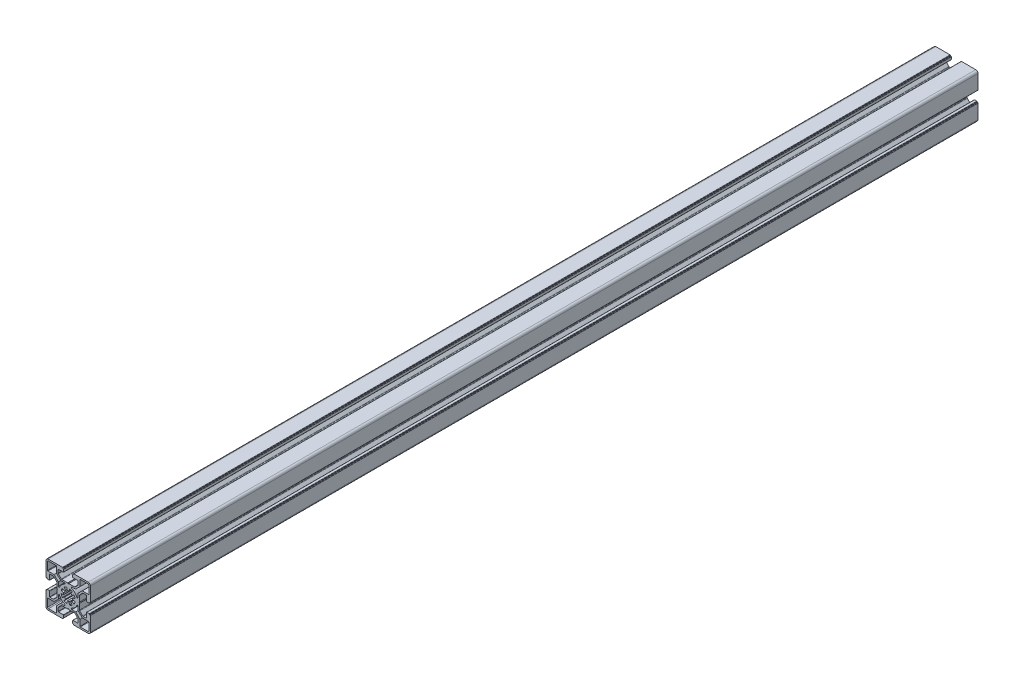
SolidWorks part; units mm, degrees
material "6063 T5"
ref_plane "Спереди" through (0, 0, 0) normal (0, 0, 1) x (1, 0, 0)
ref_plane "Сверху" through (0, 0, 0) normal (0, 1, 0) x (1, 0, 0)
ref_plane "Справа" through (0, 0, 0) normal (1, 0, 0) x (0, 0, -1)
sketch "Эскиз2" plane through (0, 0, 0) normal (0, 0, 1) x (1, 0, 0)
  line L0 (0, 0) -> (-23.2, 23.2) construction
  line L1 (-11.1, 8.413) -> (-11.1, 4.1569)
  line L2 (-11.1, 8.413) -> (-15.887, 13.2)
  line L3 (-8.413, 11.1) -> (-13.2, 15.887)
  line L4 (-8.413, 11.1) -> (-4.1569, 11.1)
  line L17 (-25, 11.3) -> (-25, 22.5)
  line L18 (-22.5, 25) -> (-11.3, 25)
  line L19 (11.3, 25) -> (22.5, 25)
  line L20 (25, 22.5) -> (25, 11.3)
  line L21 (25, -11.3) -> (25, -22.5)
  line L22 (22.5, -25) -> (11.3, -25)
  line L23 (-11.3, -25) -> (-22.5, -25)
  line L24 (-25, -22.5) -> (-25, -11.3)
  line L25 (-25.0176, 33.1253) -> (24.9824, 33.1253) construction
  line L26 (-15.887, 13.2) -> (-22.7, 13.2)
  line L27 (-23.2, 13.7) -> (-23.2, 22.2)
  line L28 (-22.2, 23.2) -> (-13.7, 23.2)
  line L29 (-13.2, 22.7) -> (-13.2, 15.887)
  line L30 (22.7, 13.2) -> (15.887, 13.2)
  line L31 (11.1, 8.413) -> (15.887, 13.2) [skipped]
  line L32 (11.1, 8.413) -> (11.1, 4.1569) [skipped]
  line L33 (8.413, 11.1) -> (4.1569, 11.1) [skipped]
  line L34 (8.413, 11.1) -> (13.2, 15.887) [skipped]
  line L35 (8.413, -11.1) -> (13.2, -15.887) [skipped]
  line L36 (8.413, -11.1) -> (4.1569, -11.1) [skipped]
  line L37 (11.1, -8.413) -> (11.1, -4.1569) [skipped]
  line L38 (11.1, -8.413) -> (15.887, -13.2) [skipped]
  line L39 (-11.1, -8.413) -> (-15.887, -13.2) [skipped]
  line L40 (-11.1, -8.413) -> (-11.1, -4.1569) [skipped]
  line L41 (-8.413, -11.1) -> (-4.1569, -11.1) [skipped]
  line L42 (-8.413, -11.1) -> (-13.2, -15.887) [skipped]
  line L43 (11.1, 8.413) -> (15.887, 13.2)
  line L44 (11.1, 8.413) -> (11.1, 4.1569)
  line L45 (8.413, 11.1) -> (4.1569, 11.1)
  line L46 (8.413, 11.1) -> (13.2, 15.887)
  line L47 (13.2, 15.887) -> (13.2, 22.7)
  line L48 (13.7, 23.2) -> (22.2, 23.2)
  line L49 (23.2, 22.2) -> (23.2, 13.7)
  line L50 (13.2, -22.7) -> (13.2, -15.887)
  line L51 (8.413, -11.1) -> (13.2, -15.887)
  line L52 (8.413, -11.1) -> (4.1569, -11.1)
  line L53 (11.1, -8.413) -> (11.1, -4.1569)
  line L54 (11.1, -8.413) -> (15.887, -13.2)
  line L55 (15.887, -13.2) -> (22.7, -13.2)
  line L56 (23.2, -13.7) -> (23.2, -22.2)
  line L57 (22.2, -23.2) -> (13.7, -23.2)
  line L58 (-22.7, -13.2) -> (-15.887, -13.2)
  line L59 (-11.1, -8.413) -> (-15.887, -13.2)
  line L60 (-11.1, -8.413) -> (-11.1, -4.1569)
  line L61 (-8.413, -11.1) -> (-4.1569, -11.1)
  line L62 (-8.413, -11.1) -> (-13.2, -15.887)
  line L63 (-13.2, -15.887) -> (-13.2, -22.7)
  line L64 (-13.7, -23.2) -> (-22.2, -23.2)
  line L65 (-23.2, -22.2) -> (-23.2, -13.7)
  arc A2 (-3.8971, 9.75) -> (-9.75, 3.8971) centre (0, 0) ccw
  arc A3 (-9.75, 3.8971) -> (-11.1, 4.1569) centre (-10.4, 4.1569) cw
  arc A5 (-3.8971, 9.75) -> (-4.1569, 11.1) centre (-4.1569, 10.4) ccw
  arc A18 (-25, 22.5) -> (-22.5, 25) centre (-22.5, 22.5) cw
  arc A19 (22.5, 25) -> (25, 22.5) centre (22.5, 22.5) cw
  arc A20 (25, -22.5) -> (22.5, -25) centre (22.5, -22.5) cw
  arc A21 (-22.5, -25) -> (-25, -22.5) centre (-22.5, -22.5) cw
  arc A22 (-23.2, 22.2) -> (-22.2, 23.2) centre (-22.2, 22.2) cw
  arc A23 (-13.7, 23.2) -> (-13.2, 22.7) centre (-13.7, 22.7) cw
  arc A24 (-22.7, 13.2) -> (-23.2, 13.7) centre (-22.7, 13.7) cw
  arc A25 (9.75, 3.8971) -> (11.1, 4.1569) centre (10.4, 4.1569) ccw [skipped]
  arc A26 (9.75, 3.8971) -> (3.8971, 9.75) centre (0, 0) ccw [skipped]
  arc A27 (3.8971, 9.75) -> (4.1569, 11.1) centre (4.1569, 10.4) cw [skipped]
  arc A28 (3.8971, -9.75) -> (4.1569, -11.1) centre (4.1569, -10.4) ccw [skipped]
  arc A29 (3.8971, -9.75) -> (9.75, -3.8971) centre (0, 0) ccw [skipped]
  arc A30 (9.75, -3.8971) -> (11.1, -4.1569) centre (10.4, -4.1569) cw [skipped]
  arc A31 (-9.75, -3.8971) -> (-11.1, -4.1569) centre (-10.4, -4.1569) ccw [skipped]
  arc A32 (-9.75, -3.8971) -> (-3.8971, -9.75) centre (0, 0) ccw [skipped]
  arc A33 (-3.8971, -9.75) -> (-4.1569, -11.1) centre (-4.1569, -10.4) cw [skipped]
  arc A34 (9.75, 3.8971) -> (11.1, 4.1569) centre (10.4, 4.1569) ccw
  arc A35 (9.75, 3.8971) -> (3.8971, 9.75) centre (0, 0) ccw
  arc A36 (3.8971, 9.75) -> (4.1569, 11.1) centre (4.1569, 10.4) cw
  arc A37 (13.2, 22.7) -> (13.7, 23.2) centre (13.7, 22.7) cw
  arc A38 (22.2, 23.2) -> (23.2, 22.2) centre (22.2, 22.2) cw
  arc A39 (23.2, 13.7) -> (22.7, 13.2) centre (22.7, 13.7) cw
  arc A40 (3.8971, -9.75) -> (4.1569, -11.1) centre (4.1569, -10.4) ccw
  arc A41 (3.8971, -9.75) -> (9.75, -3.8971) centre (0, 0) ccw
  arc A42 (9.75, -3.8971) -> (11.1, -4.1569) centre (10.4, -4.1569) cw
  arc A43 (22.7, -13.2) -> (23.2, -13.7) centre (22.7, -13.7) cw
  arc A44 (23.2, -22.2) -> (22.2, -23.2) centre (22.2, -22.2) cw
  arc A45 (13.7, -23.2) -> (13.2, -22.7) centre (13.7, -22.7) cw
  arc A46 (-9.75, -3.8971) -> (-11.1, -4.1569) centre (-10.4, -4.1569) ccw
  arc A47 (-9.75, -3.8971) -> (-3.8971, -9.75) centre (0, 0) ccw
  arc A48 (-3.8971, -9.75) -> (-4.1569, -11.1) centre (-4.1569, -10.4) cw
  arc A49 (-13.2, -22.7) -> (-13.7, -23.2) centre (-13.7, -22.7) cw
  arc A50 (-22.2, -23.2) -> (-23.2, -22.2) centre (-22.2, -22.2) cw
  arc A51 (-23.2, -13.7) -> (-22.7, -13.2) centre (-22.7, -13.7) cw
  point P50 (0, 0)
  point P71 (0, 0)
  point P84 (-23.2, 13.2)
  point P155 (0, 0)
  line B0 (-25, 11.3) -> (-25, 6.4)
  line B1 (-24.7, 6.1) -> (-24, 6.1)
  line B2 (-24, 6.1) -> (-24, 5.4)
  line B3 (-23.7, 5.1) -> (-21.1, 5.1)
  line B4 (-20.8, 5.4) -> (-20.8, 11)
  line B5 (-20.5, 11.3) -> (-16.9142, 11.3)
  line B6 (-16.2071, 11.0071) -> (-12.9929, 7.7929)
  line B7 (-12.7, 7.0858) -> (-12.7, 0.6)
  line B8 (-12.7, 0) -> (-25, 0) construction
  line B9 (-16.2071, -11.0071) -> (-12.9929, -7.7929)
  line B10 (-20.5, -11.3) -> (-16.9142, -11.3)
  line B11 (-20.8, -5.4) -> (-20.8, -11)
  line B12 (-23.7, -5.1) -> (-21.1, -5.1)
  line B13 (-24, -6.1) -> (-24, -5.4)
  line B14 (-24.7, -6.1) -> (-24, -6.1)
  line B15 (-25, -11.3) -> (-25, -6.4)
  line B16 (-12.7, 0.6) -> (-12.1, 0)
  line B17 (-12.1, 0) -> (-12.7, -0.6)
  line B18 (-12.7, -0.6) -> (-12.7, -7.0858)
  arc B19 (-21.1, 5.1) -> (-20.8, 5.4) centre (-21.1, 5.4) ccw
  arc B20 (-24, 5.4) -> (-23.7, 5.1) centre (-23.7, 5.4) ccw
  arc B21 (-25, 6.4) -> (-24.7, 6.1) centre (-24.7, 6.4) ccw
  arc B22 (-12.9929, 7.7929) -> (-12.7, 7.0858) centre (-13.7, 7.0858) cw
  arc B23 (-16.9142, 11.3) -> (-16.2071, 11.0071) centre (-16.9142, 10.3) cw
  arc B24 (-16.9142, -11.3) -> (-16.2071, -11.0071) centre (-16.9142, -10.3) ccw
  arc B25 (-12.9929, -7.7929) -> (-12.7, -7.0858) centre (-13.7, -7.0858) ccw
  arc B26 (-25, -6.4) -> (-24.7, -6.1) centre (-24.7, -6.4) cw
  arc B27 (-24, -5.4) -> (-23.7, -5.1) centre (-23.7, -5.4) cw
  arc B28 (-21.1, -5.1) -> (-20.8, -5.4) centre (-21.1, -5.4) cw
  arc B29 (-20.5, -11.3) -> (-20.8, -11) centre (-20.5, -11) cw
  arc B30 (-20.8, 11) -> (-20.5, 11.3) centre (-20.5, 11) cw
  line B31 (0, 0) -> (3.6062, 3.6062) construction
  line B32 (1.4579, 7.866) -> (0.9294, 5.0146)
  line B33 (2.8887, 4.203) -> (4.5312, 6.593)
  line B34 (0, 0) -> (0, 5.1) construction
  arc B35 (0.9294, -5.0146) -> (-0.9294, -5.0146) centre (0, 0) cw
  arc B36 (-6.593, -4.5312) -> (-7.866, -1.4579) centre (0, 0) cw
  arc B37 (4.203, 2.8887) -> (2.8887, 4.203) centre (0, 0) ccw
  arc B38 (4.5312, 6.593) -> (1.4579, 7.866) centre (0, 0) ccw
  arc B39 (0.9294, 5.0146) -> (-0.9294, 5.0146) centre (0, 0) ccw
  line B40 (-1.4579, 7.866) -> (-0.9294, 5.0146)
  arc B41 (4.5312, -6.593) -> (1.4579, -7.866) centre (0, 0) cw
  arc B42 (-4.203, -2.8887) -> (-2.8887, -4.203) centre (0, 0) ccw
  line B43 (-2.8887, -4.203) -> (-4.5312, -6.593)
  line B44 (0, 0) -> (6.3318, 0) construction
  line B45 (4.203, 2.8887) -> (6.593, 4.5312)
  line B46 (7.866, 1.4579) -> (5.0146, 0.9294)
  line B47 (-7.866, 1.4579) -> (-5.0146, 0.9294)
  line B48 (-4.203, 2.8887) -> (-6.593, 4.5312)
  line B49 (-2.8887, 4.203) -> (-4.5312, 6.593)
  line B50 (7.866, -1.4579) -> (5.0146, -0.9294)
  line B51 (4.203, -2.8887) -> (6.593, -4.5312)
  line B52 (2.8887, -4.203) -> (4.5312, -6.593)
  line B53 (1.4579, -7.866) -> (0.9294, -5.0146)
  line B54 (-1.4579, -7.866) -> (-0.9294, -5.0146)
  line B55 (-4.203, -2.8887) -> (-6.593, -4.5312)
  line B56 (-7.866, -1.4579) -> (-5.0146, -0.9294)
  arc B57 (5.0146, 0.9294) -> (5.0146, -0.9294) centre (0, 0) cw
  arc B58 (6.593, 4.5312) -> (7.866, 1.4579) centre (0, 0) cw
  arc B59 (-5.0146, 0.9294) -> (-5.0146, -0.9294) centre (0, 0) ccw
  arc B60 (-6.593, 4.5312) -> (-7.866, 1.4579) centre (0, 0) ccw
  arc B61 (-4.203, 2.8887) -> (-2.8887, 4.203) centre (0, 0) cw
  arc B62 (-4.5312, 6.593) -> (-1.4579, 7.866) centre (0, 0) cw
  arc B63 (6.593, -4.5312) -> (7.866, -1.4579) centre (0, 0) ccw
  arc B64 (4.203, -2.8887) -> (2.8887, -4.203) centre (0, 0) cw
  arc B65 (-4.5312, -6.593) -> (-1.4579, -7.866) centre (0, 0) ccw
  line B66 (11.3, 25) -> (6.4, 25)
  line B67 (6.1, 24.7) -> (6.1, 24)
  line B68 (6.1, 24) -> (5.4, 24)
  line B69 (5.1, 23.7) -> (5.1, 21.1)
  line B70 (5.4, 20.8) -> (11, 20.8)
  line B71 (11.3, 20.5) -> (11.3, 16.9142)
  line B72 (11.0071, 16.2071) -> (7.7929, 12.9929)
  line B73 (7.0858, 12.7) -> (0.6, 12.7)
  line B74 (0, 12.7) -> (0, 25) construction
  line B75 (-11.0071, 16.2071) -> (-7.7929, 12.9929)
  line B76 (-11.3, 20.5) -> (-11.3, 16.9142)
  line B77 (-5.4, 20.8) -> (-11, 20.8)
  line B78 (-5.1, 23.7) -> (-5.1, 21.1)
  line B79 (-6.1, 24) -> (-5.4, 24)
  line B80 (-6.1, 24.7) -> (-6.1, 24)
  line B81 (-11.3, 25) -> (-6.4, 25)
  line B82 (0.6, 12.7) -> (0, 12.1)
  line B83 (0, 12.1) -> (-0.6, 12.7)
  line B84 (-0.6, 12.7) -> (-7.0858, 12.7)
  arc B85 (5.1, 21.1) -> (5.4, 20.8) centre (5.4, 21.1) ccw
  arc B86 (5.4, 24) -> (5.1, 23.7) centre (5.4, 23.7) ccw
  arc B87 (6.4, 25) -> (6.1, 24.7) centre (6.4, 24.7) ccw
  arc B88 (7.7929, 12.9929) -> (7.0858, 12.7) centre (7.0858, 13.7) cw
  arc B89 (11.3, 16.9142) -> (11.0071, 16.2071) centre (10.3, 16.9142) cw
  arc B90 (-11.3, 16.9142) -> (-11.0071, 16.2071) centre (-10.3, 16.9142) ccw
  arc B91 (-7.7929, 12.9929) -> (-7.0858, 12.7) centre (-7.0858, 13.7) ccw
  arc B92 (-6.4, 25) -> (-6.1, 24.7) centre (-6.4, 24.7) cw
  arc B93 (-5.4, 24) -> (-5.1, 23.7) centre (-5.4, 23.7) cw
  arc B94 (-5.1, 21.1) -> (-5.4, 20.8) centre (-5.4, 21.1) cw
  arc B95 (-11.3, 20.5) -> (-11, 20.8) centre (-11, 20.5) cw
  arc B96 (11, 20.8) -> (11.3, 20.5) centre (11, 20.5) cw
  line B97 (25, -11.3) -> (25, -6.4)
  line B98 (24.7, -6.1) -> (24, -6.1)
  line B99 (24, -6.1) -> (24, -5.4)
  line B100 (23.7, -5.1) -> (21.1, -5.1)
  line B101 (20.8, -5.4) -> (20.8, -11)
  line B102 (20.5, -11.3) -> (16.9142, -11.3)
  line B103 (16.2071, -11.0071) -> (12.9929, -7.7929)
  line B104 (12.7, -7.0858) -> (12.7, -0.6)
  line B105 (12.7, 0) -> (25, 0) construction
  line B106 (16.2071, 11.0071) -> (12.9929, 7.7929)
  line B107 (20.5, 11.3) -> (16.9142, 11.3)
  line B108 (20.8, 5.4) -> (20.8, 11)
  line B109 (23.7, 5.1) -> (21.1, 5.1)
  line B110 (24, 6.1) -> (24, 5.4)
  line B111 (24.7, 6.1) -> (24, 6.1)
  line B112 (25, 11.3) -> (25, 6.4)
  line B113 (12.7, -0.6) -> (12.1, 0)
  line B114 (12.1, 0) -> (12.7, 0.6)
  line B115 (12.7, 0.6) -> (12.7, 7.0858)
  arc B116 (21.1, -5.1) -> (20.8, -5.4) centre (21.1, -5.4) ccw
  arc B117 (24, -5.4) -> (23.7, -5.1) centre (23.7, -5.4) ccw
  arc B118 (25, -6.4) -> (24.7, -6.1) centre (24.7, -6.4) ccw
  arc B119 (12.9929, -7.7929) -> (12.7, -7.0858) centre (13.7, -7.0858) cw
  arc B120 (16.9142, -11.3) -> (16.2071, -11.0071) centre (16.9142, -10.3) cw
  arc B121 (16.9142, 11.3) -> (16.2071, 11.0071) centre (16.9142, 10.3) ccw
  arc B122 (12.9929, 7.7929) -> (12.7, 7.0858) centre (13.7, 7.0858) ccw
  arc B123 (25, 6.4) -> (24.7, 6.1) centre (24.7, 6.4) cw
  arc B124 (24, 5.4) -> (23.7, 5.1) centre (23.7, 5.4) cw
  arc B125 (21.1, 5.1) -> (20.8, 5.4) centre (21.1, 5.4) cw
  arc B126 (20.5, 11.3) -> (20.8, 11) centre (20.5, 11) cw
  arc B127 (20.8, -11) -> (20.5, -11.3) centre (20.5, -11) cw
  line B128 (-11.3, -25) -> (-6.4, -25)
  line B129 (-6.1, -24.7) -> (-6.1, -24)
  line B130 (-6.1, -24) -> (-5.4, -24)
  line B131 (-5.1, -23.7) -> (-5.1, -21.1)
  line B132 (-5.4, -20.8) -> (-11, -20.8)
  line B133 (-11.3, -20.5) -> (-11.3, -16.9142)
  line B134 (-11.0071, -16.2071) -> (-7.7929, -12.9929)
  line B135 (-7.0858, -12.7) -> (-0.6, -12.7)
  line B136 (0, -12.7) -> (0, -25) construction
  line B137 (11.0071, -16.2071) -> (7.7929, -12.9929)
  line B138 (11.3, -20.5) -> (11.3, -16.9142)
  line B139 (5.4, -20.8) -> (11, -20.8)
  line B140 (5.1, -23.7) -> (5.1, -21.1)
  line B141 (6.1, -24) -> (5.4, -24)
  line B142 (6.1, -24.7) -> (6.1, -24)
  line B143 (11.3, -25) -> (6.4, -25)
  line B144 (-0.6, -12.7) -> (0, -12.1)
  line B145 (0, -12.1) -> (0.6, -12.7)
  line B146 (0.6, -12.7) -> (7.0858, -12.7)
  arc B147 (-5.1, -21.1) -> (-5.4, -20.8) centre (-5.4, -21.1) ccw
  arc B148 (-5.4, -24) -> (-5.1, -23.7) centre (-5.4, -23.7) ccw
  arc B149 (-6.4, -25) -> (-6.1, -24.7) centre (-6.4, -24.7) ccw
  arc B150 (-7.7929, -12.9929) -> (-7.0858, -12.7) centre (-7.0858, -13.7) cw
  arc B151 (-11.3, -16.9142) -> (-11.0071, -16.2071) centre (-10.3, -16.9142) cw
  arc B152 (11.3, -16.9142) -> (11.0071, -16.2071) centre (10.3, -16.9142) ccw
  arc B153 (7.7929, -12.9929) -> (7.0858, -12.7) centre (7.0858, -13.7) ccw
  arc B154 (6.4, -25) -> (6.1, -24.7) centre (6.4, -24.7) cw
  arc B155 (5.4, -24) -> (5.1, -23.7) centre (5.4, -23.7) cw
  arc B156 (5.1, -21.1) -> (5.4, -20.8) centre (5.4, -21.1) cw
  arc B157 (11.3, -20.5) -> (11, -20.8) centre (11, -20.5) cw
  arc B158 (-11, -20.8) -> (-11.3, -20.5) centre (-11, -20.5) cw
  dimension "D1" = 25
  dimension "D2" = 45
  dimension "D3" = 0.7
  dimension "D4" = 10.5
  dimension "D7" = 4
  dimension "D9" = 2.5
  dimension "D13" = 1
  dimension "D14" = 0.5
  dimension "D5" = 1.6
  dimension "D6" = 1.9
  dimension "D8" = 10
  dimension "D10" = 50
  dimension "D12" = 1.8
  dimension "D11" = 4
  dimension "D15" = 4
sketch_block_instance "8B(20,5PL_cut)-1"
sketch_block "8B(20,5PL_cut)" parameters "D7"=0.3, "D8"=1, "D12"=0.3, "D10"=0.3, "D1"=12.3, "D2"=4.2, "D3"=10.2, "D4"=22.6, "D5"=12.2, "D6"=135, "D9"=1, "D11"=2.5, "D13"=1.2, "D14"=11.8
sketch_block_instance "Блок1-1"
sketch_block "Блок1" parameters "D1"=10.2, "D5"=16, "D2"=10.5, "D3"=24, "D4"=45
sketch_block_instance "8B(20,5PL_cut)-4"
sketch_block_instance "8B(20,5PL_cut)-5"
sketch_block_instance "8B(20,5PL_cut)-6"
extrude "Бобышка-Вытянуть2" add sketch "Эскиз2" along normal blind 1000 contours B156 B140 B155 B141 B142 B154 B143 L22 A20 L21 B97 B118 B98 B99 B117 B100 B116 B101 B127 B102 B120 B103 B119 B104 B113 B114 B115 B122 B106 B121 B107 B126 B108 B125 B109 B124 B110 B111 B123 B112 L20 A19 L19 B66 B87 B67 B68 B86 B69 B85 B70
